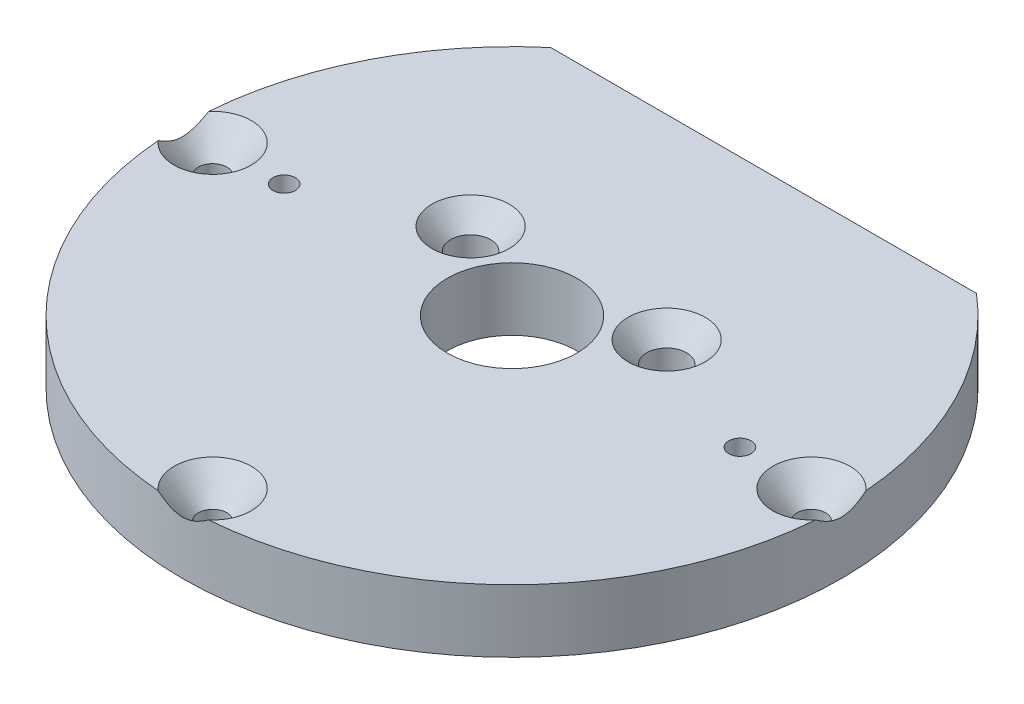
SolidWorks part; units mm, degrees
ref_plane "Front Plane" through (0, 0, 0) normal (0, 0, 1) x (1, 0, 0)
ref_plane "Top Plane" through (0, 0, 0) normal (0, 1, 0) x (1, 0, 0)
ref_plane "Right Plane" through (0, 0, 0) normal (1, 0, 0) x (0, 0, -1)
sketch "Sketch1" plane through (0, 0, 0) normal (0, 1, 0) x (1, 0, 0)
  circle A0 centre (0, 0) radius 33.274
  dimension "D1" = 66.548
extrude "Boss-Extrude1" add sketch "Sketch1" along normal blind 6.35
hole_wizard "PlateMtgScrew" positions "Sketch6" profile "Sketch7" tap size "#6-40" standard "ANSI Inch"
sketch "Sketch6" plane through (0, 6.35, 0) normal (0, 1, 0) x (1, 0, 0)
  circle A0 centre (0, 0) radius 30.226 construction
  point P5 (-30.226, 0)
  point P7 (0, -30.226)
  point P9 (30.226, 0)
  dimension "D1" = 60.452
sketch "Sketch7" plane through (30.226, 6.35, 0) normal (1, 0, 0) x (0, 0, 1)
  line L0 (0, 0) -> (0, 11.0477)
  line L1 (0, 11.0477) -> (1.4351, 10.1854)
  line L2 (1.4351, 10.1854) -> (1.4351, 2.8343)
  line L3 (1.4351, 2.8343) -> (3.8989, 0)
  line L5 (3.8989, 0) -> (0, 0)
  line L6 (-1.4351, 2.8343) -> (-3.8989, 0) construction
  line L10 (0, 11.0477) -> (-1.4351, 10.1854) construction
  line L11 (0, -6.35) -> (0, 107.95) construction
  dimension "Tap Drill Dia." = 2.8702
  dimension "Tap Drill Depth" = 10.1854
  dimension "Near C'Sink Dia." = 7.7978
  dimension "Near C'Sink Angle" = 82
  dimension "Drill Angle" = 118
cosmetic thread "Hole Thread8" parameters "D1"=7.0104, "D2"=3.5052
cosmetic thread "Hole Thread9" parameters "D1"=7.0104, "D2"=3.5052
cosmetic thread "Hole Thread10" parameters "D1"=7.0104, "D2"=3.5052
hole_wizard "EncoderMtgHoles" positions "Sketch8" profile "Sketch9" tap size "#4-40" standard "ANSI Inch" end condition through all
sketch "Sketch8" plane through (0, 6.35, 0) normal (0, 1, 0) x (1, 0, 0)
  point P0 (23.0124, 0)
  point P2 (-23.0124, 0)
  dimension "D1" = 46.0248
  dimension "D2" = 23.0124
sketch "Sketch9" plane through (23.0124, 6.35, 0) normal (1, 0, 0) x (0, 0, 1)
  line L0 (0, 0) -> (0, 6.35)
  line L1 (0, 6.35) -> (1.1303, 6.35)
  line L2 (1.1303, 6.35) -> (1.1303, 0)
  line L5 (1.1303, 0) -> (0, 0)
  line L11 (0, -6.35) -> (0, 107.95) construction
  dimension "Thru Tap Drill Dia." = 2.2606
  dimension "Thru Tap Drill Depth" = 6.35
cosmetic thread "Hole Thread4" parameters "D2"=2.8448
cosmetic thread "Hole Thread5" parameters "D2"=2.8448
hole_wizard "SlipRgShftClr" positions "Sketch10" profile "Sketch11" legacy end condition through all
sketch "Sketch10" plane through (0, 6.35, 0) normal (0, 1, 0) x (1, 0, 0)
  point P0 (0, 0)
sketch "Sketch11" plane through (0, 6.35, 0) normal (1, 0, 0) x (0, 0, 1)
  line L0 (0, 0) -> (0, 10.2845)
  line L1 (0, 10.2845) -> (6.5481, 6.35)
  line L2 (6.5481, 6.35) -> (6.5481, 0)
  line L4 (6.5481, 0) -> (0, 0)
  line L6 (0, 10.2845) -> (-6.5481, 6.35) construction
  line L7 (0, -4.2442) -> (0, 117.3081) construction
  dimension "Diameter" = 13.0962
  dimension "Depth" = 6.35
  dimension "Drill Angle" = 118
sketch "Sketch12" plane through (0, 6.35, 0) normal (0, 1, 0) x (1, 0, 0)
  line L0 (0, 0) -> (35.5286, 20.5125) construction
  line L1 (0, 0) -> (47.3784, 0) construction
  line L2 (0, 0) -> (-39.4254, 0) construction
  line L3 (0, 0) -> (-39.7451, 22.9469) construction
  circle A0 centre (0, 0) radius 11.43 construction
  dimension "D1" = 22.86
  dimension "D2" = 30
  dimension "D3" = 30
hole_wizard "Additional Holes" positions "Sketch15" profile "Sketch14" tap size "#10-32" standard "ANSI Inch" end condition through all
sketch "Sketch15" plane through (0, 6.35, 0) normal (0, 1, 0) x (1, 0, 0)
  line L0 (0, 0) -> (-39.7451, 22.9469) construction
  line L1 (0, 0) -> (35.5286, 20.5125) construction
  circle A0 centre (0, 0) radius 11.43 construction
  point P0 (-9.8987, 5.715)
  point P6 (9.8987, 5.715)
sketch "Sketch14" plane through (-9.8987, 6.35, -5.715) normal (1, 0, 0) x (0, 0, 1)
  line L0 (0, 0) -> (0, 6.35)
  line L1 (0, 6.35) -> (2.0193, 6.35)
  line L2 (2.0193, 6.35) -> (2.0193, 2.1622)
  line L3 (2.0193, 2.1622) -> (3.8989, 0)
  line L5 (3.8989, 0) -> (0, 0)
  line L6 (-2.0193, 2.1622) -> (-3.8989, 0) construction
  line L11 (0, -6.35) -> (0, 107.95) construction
  dimension "Thru Tap Drill Dia." = 4.0386
  dimension "Thru Tap Drill Depth" = 6.35
  dimension "Near C'Sink Dia." = 7.7978
  dimension "Near C'Sink Angle" = 82
cosmetic thread "Hole Thread11" parameters "D2"=4.826
cosmetic thread "Hole Thread12" parameters "D2"=4.826
sketch "Sketch16" plane through (0, 6.35, 0) normal (0, 1, 0) x (1, 0, 0)
  line L0 (-21.4942, 25.4) -> (21.4942, 25.4)
  circle A0 centre (0, 0) radius 33.274 construction
  dimension "D1" = 25.4
extrude "Cut-Extrude1" cut sketch "Sketch16" against normal through all
